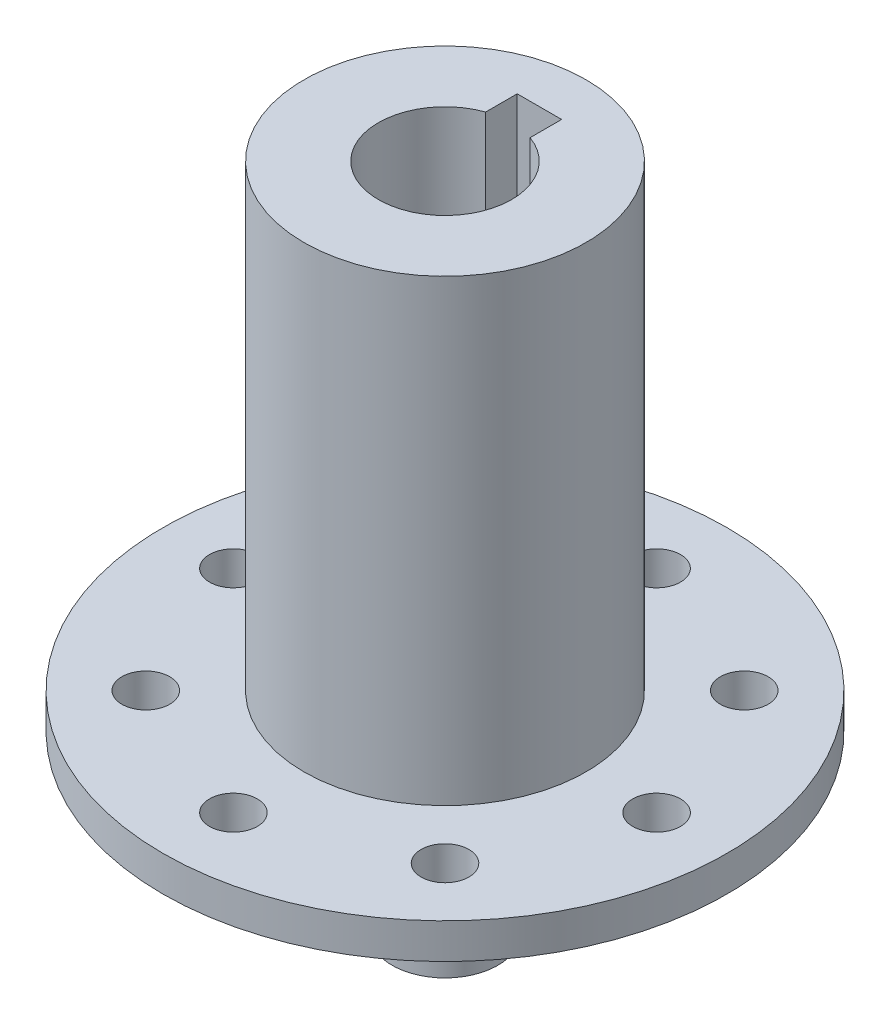
SolidWorks part; units mm, degrees
material "6061-T6 (SS)"
ref_plane "Front Plane" through (0, 0, 0) normal (0, 0, 1) x (1, 0, 0)
ref_plane "Top Plane" through (0, 0, 0) normal (0, 1, 0) x (1, 0, 0)
ref_plane "Right Plane" through (0, 0, 0) normal (1, 0, 0) x (0, 0, -1)
sketch "Sketch1" plane through (0, 0, 0) normal (0, 1, 0) x (1, 0, 0)
  line L0 (-2, 5.6569) -> (-2, 8.5) construction
  line L1 (-2, 8.5) -> (2, 8.5) construction
  line L3 (-2, 3.5) -> (2, 3.5) construction
  line L5 (2, 5.6569) -> (2, 8.5) construction
  circle A0 centre (0, 0) radius 22.225 construction
  circle A2 centre (0, 0) radius 12.7
  point P8 (0, 8.5)
  point P10 (0, -6)
  point P11 (-2, 5.6569)
  point P12 (2, 5.6569)
  dimension "D1" = 44.45
  dimension "D6" = 25.4
  dimension "D3" = 4
  dimension "D4" = 5
  dimension "D5" = 9.5
extrude "Boss-Extrude1" add sketch "Sketch1" along normal blind 41.275
sketch "Sketch2" plane through (0, 0, 0) normal (0, -1, 0) x (1, 0, 0)
  circle A0 centre (0, 0) radius 25.4
  circle A3 centre (0, 0) radius 12.7
  dimension "D1" = 50.8
  dimension "D2" = 25.4
sketch "Sketch3" plane through (0, 0, 0) normal (0, -1, 0) x (1, 0, 0)
  circle A1 centre (0, 0) radius 25.4
  point P4 (0, 0)
  dimension "D1" = 50.8
extrude "Boss-Extrude3" add sketch "Sketch3" along normal blind 3.175
sketch "Sketch4" plane through (0, -3.175, 0) normal (0, -1, 0) x (1, 0, 0)
  line L0 (0, 19.05) -> (0, -19.05) construction
  line L1 (19.05, 0) -> (-19.05, 0) construction
  line L2 (13.4704, 13.4704) -> (-13.4704, -13.4704) construction
  line L3 (-13.4704, 13.4704) -> (13.4704, -13.4704) construction
  point P6 (0, 0)
  point P7 (0, 0)
  point P10 (0, 0)
  point P13 (0, 0)
  dimension "D1" = 45
  dimension "D2" = 45
  dimension "D3" = 38.1
hole_wizard "#8 Clearance Hole1" positions "Sketch5" profile "Sketch6" hole size "#8" standard "ANSI Inch" end condition through all
sketch "Sketch5" plane through (0, -3.175, 0) normal (0, -1, 0) x (-1, 0, 0)
  point P0 (0, 19.05)
  point P3 (-13.4704, 13.4704)
  point P6 (-19.05, 0)
  point P9 (-13.4704, -13.4704)
  point P12 (0, -19.05)
  point P15 (13.4704, -13.4704)
  point P18 (19.05, 0)
  point P21 (13.4704, 13.4704)
sketch "Sketch6" plane through (0, -3.175, -19.05) normal (1, 0, 0) x (0, 0, -1)
  line L0 (0, 0) -> (0, 44.45)
  line L1 (0, 44.45) -> (2.1526, 44.45)
  line L2 (2.1526, 44.45) -> (2.1526, 0)
  line L5 (2.1526, 0) -> (0, 0)
  line L11 (0, -6.35) -> (0, 107.95) construction
  dimension "Thru Hole Dia." = 4.3053
  dimension "Thru Hole Depth" = 44.45
sketch "Sketch7" plane through (0, 41.275, 0) normal (0, 1, 0) x (1, 0, 0)
  line L0 (-2, 5.6569) -> (-2, 3.5) construction
  line L1 (-2, 8.5) -> (2, 8.5)
  line L2 (-2, 8.5) -> (-2, 5.6569)
  line L4 (2, 8.5) -> (2, 5.6569)
  line L5 (-2, 3.5) -> (2, 3.5) construction
  line L6 (2, 3.5) -> (2, 5.6569) construction
  arc A2 (-2, 5.6569) -> (2, 5.6569) centre (0, 0) ccw
  arc A3 (-2, 5.6569) -> (2, 5.6569) centre (0, 0) cw construction
  point P1 (0, 8.5)
  point P8 (0, -6)
  point P11 (0, 6)
  dimension "D4" = 12
  dimension "D1" = 14.5
  dimension "D2" = 9.5
  dimension "D3" = 4
  dimension "D5" = 2.5
extrude "20.8mmToEndofKeyway" cut sketch "Sketch7" against normal blind 22.0625
sketch "Sketch8" plane through (0, -3.175, 0) normal (0, -1, 0) x (1, 0, 0)
  circle A0 centre (0, 0) radius 4.7625
  circle A2 centre (0, -19.05) radius 2.1526 construction
  circle A3 centre (0, -19.05) radius 2.1526 construction
  circle A4 centre (0, -19.05) radius 4.0894 construction
  dimension "D1" = 9.525
  dimension "D2" = 8.1788
extrude "Boss-Extrude4" add sketch "Sketch8" along normal blind 15.875
fillet "Fillet1" radius 5 1 edges at (0, -3.175, -4.7625)
